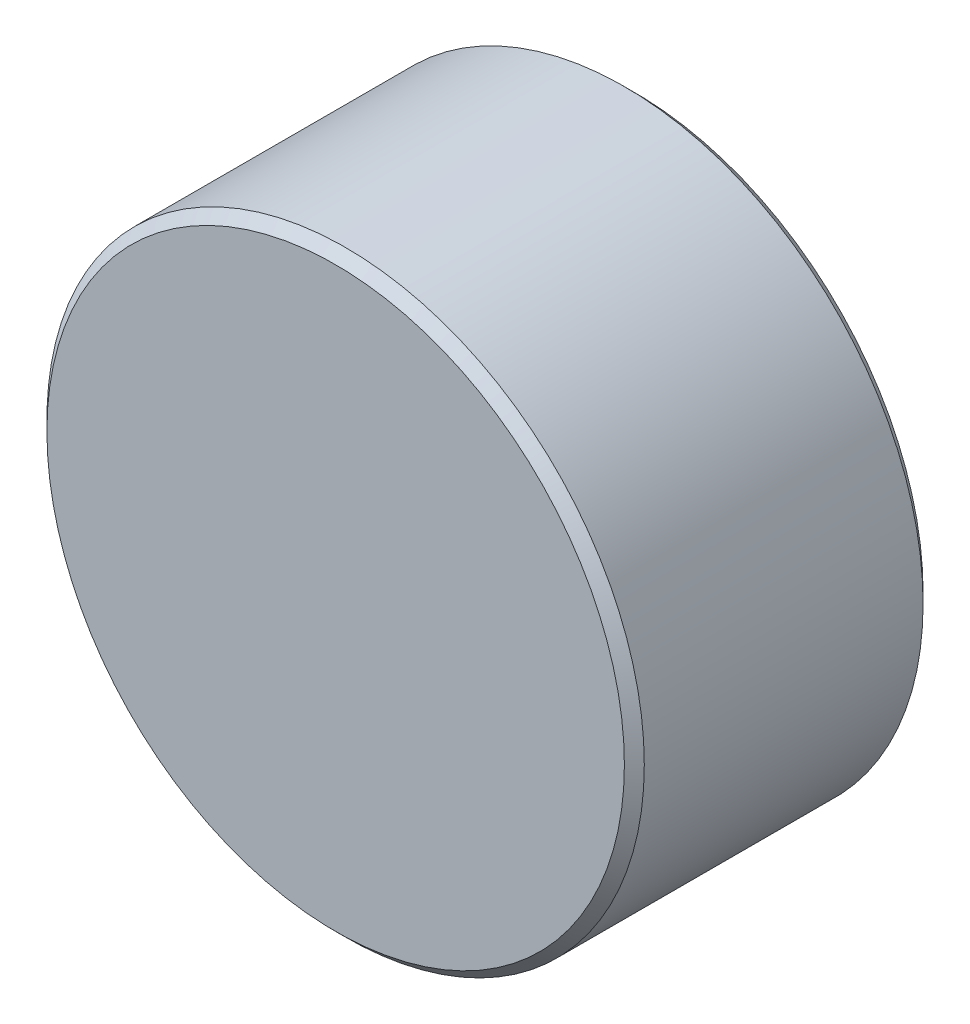
SolidWorks part; units mm, degrees
ref_plane "Front Plane" through (0, 0, 0) normal (0, 0, 1) x (1, 0, 0)
ref_plane "Top Plane" through (0, 0, 0) normal (0, 1, 0) x (1, 0, 0)
ref_plane "Right Plane" through (0, 0, 0) normal (1, 0, 0) x (0, 0, -1)
sketch "Sketch1" plane through (0, 0, 0) normal (0, 0, 1) x (1, 0, 0)
  circle A0 centre (0, 0) radius 3
  dimension "D1" = 6
extrude "Boss-Extrude1" add sketch "Sketch1" along normal blind 3
chamfer "Chamfer1" distance 0.1 angle 45 2 edges at (3, 0, 0) (3, 0, 3)
